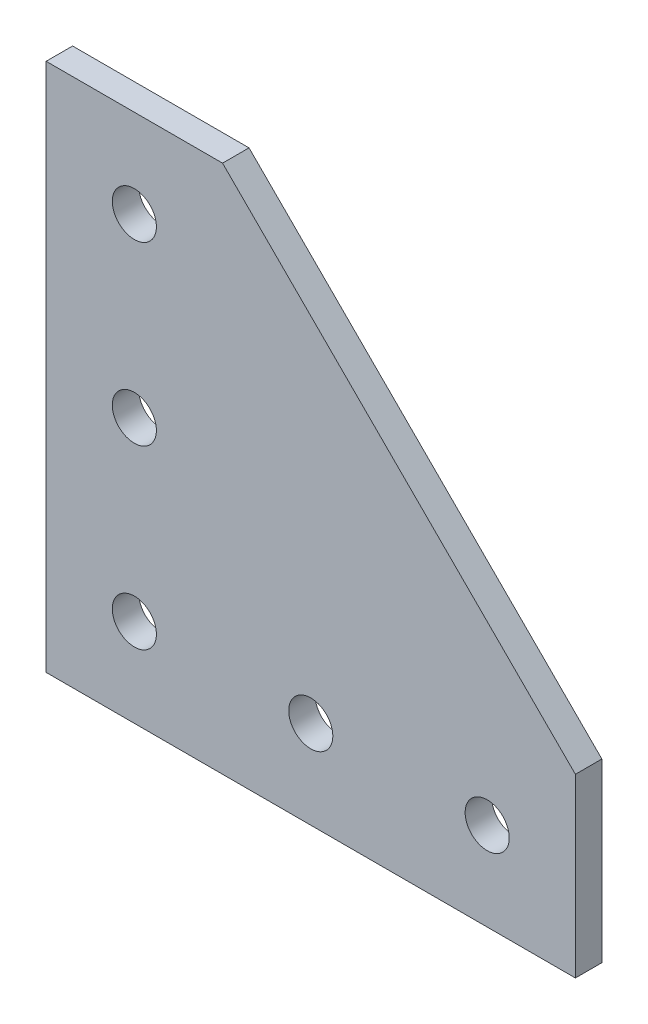
SolidWorks part; units mm, degrees
ref_plane "Front Plane" through (0, 0, 0) normal (0, 0, 1) x (1, 0, 0)
ref_plane "Top Plane" through (0, 0, 0) normal (0, 1, 0) x (1, 0, 0)
ref_plane "Right Plane" through (0, 0, 0) normal (1, 0, 0) x (0, 0, -1)
sketch "Sketch1" plane through (0, 0, 0) normal (0, 0, 1) x (1, 0, 0)
  line L0 (0, 60) -> (20, 60)
  line L1 (0, 0) -> (60, 0)
  line L2 (0, 0) -> (0, 60)
  line L3 (0, 60) -> (60, 60) construction
  line L4 (60, 0) -> (60, 60) construction
  line L5 (20, 60) -> (60, 20)
  line L6 (60, 20) -> (60, 0)
  dimension "D1" = 60
  dimension "D2" = 60
  dimension "D3" = 20
  dimension "D4" = 20
extrude "Boss-Extrude1" add sketch "Sketch1" against normal blind 3
sketch "Sketch2" plane through (0, 0, 0) normal (0, 0, 1) x (1, 0, 0)
  circle A0 centre (10, 10) radius 2.5
  circle A1 centre (30, 10) radius 2.5
  circle A2 centre (50, 10) radius 2.5
  circle A3 centre (10, 30) radius 2.5
  circle A4 centre (10, 50) radius 2.5
  dimension "D3" = 5
  dimension "D1" = 10
  dimension "D2" = 10
  dimension "D4" = 3
  dimension "D5" = 3
extrude "Cut-Extrude1" cut sketch "Sketch2" against normal blind 3 contours A4
